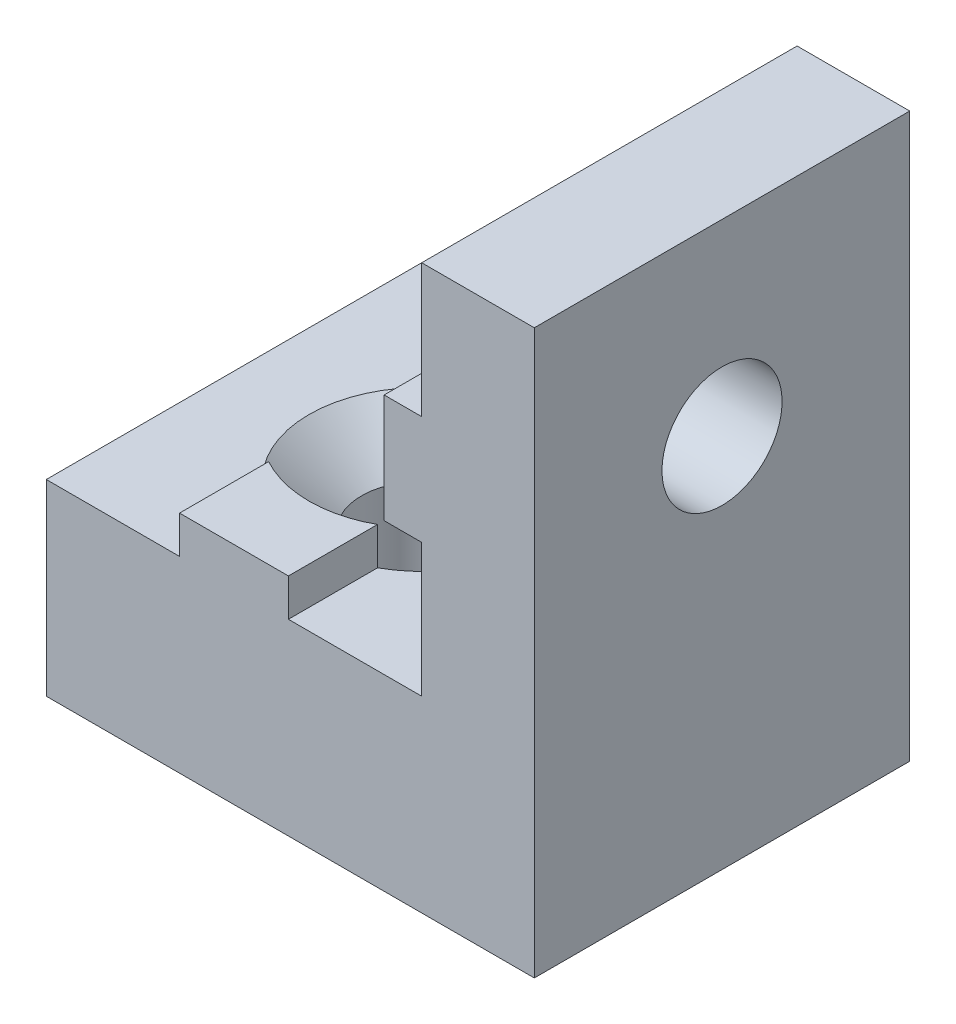
SolidWorks part; units mm, degrees
ref_plane "Front Plane" through (0, 0, 0) normal (0, 0, 1) x (1, 0, 0)
ref_plane "Top Plane" through (0, 0, 0) normal (0, 1, 0) x (1, 0, 0)
ref_plane "Right Plane" through (0, 0, 0) normal (1, 0, 0) x (0, 0, -1)
sketch "Esquisse1" plane through (0, 0, 0) normal (0, 0, 1) x (1, 0, 0)
  line L0 (0, 5) -> (3.55, 5)
  line L1 (3.55, 5) -> (3.55, 6)
  line L2 (3.55, 6) -> (6.45, 6)
  line L3 (6.45, 6) -> (6.45, 5)
  line L4 (6.45, 5) -> (10, 5)
  line L5 (10, 5) -> (10, 8.55)
  line L6 (10, 8.55) -> (9, 8.55)
  line L7 (9, 8.55) -> (9, 11.45)
  line L8 (9, 11.45) -> (10, 11.45)
  line L9 (10, 11.45) -> (10, 15)
  line L10 (10, 15) -> (13, 15)
  line L11 (13, 15) -> (13, 0)
  line L12 (13, 0) -> (0, 0)
  line L13 (0, 0) -> (0, 5)
  point P3 (-6.8358, -2.8214)
  point P15 (-7.4596, -3.1957)
  point P16 (-7.216, -1.6003)
  point P17 (0, 0)
  dimension "D1" = 3
  dimension "D2" = 3.55
  dimension "D3" = 2.9
  dimension "D4" = 5
  dimension "D5" = 1
extrude "Main" add sketch "Esquisse1" along normal blind 10
hole_wizard "Fraisage pour vis à tête fraisée (100) #01" positions "Esquisse3" profile "Esquisse4" countersink size "#0" standard "Ansi Inch"
sketch "Esquisse3" plane through (0, 5, 0) normal (0, 1, 0) x (1, 0, 0)
  line L0 (0, -10) -> (0, 0) construction
  line L1 (6.45, -10) -> (3.55, -10) construction
  point P0 (5, -5)
  dimension "D1" = 5
  dimension "D2" = 5
sketch "Esquisse4" plane through (5, 5, 5) normal (1, 0, 0) x (0, 0, 1)
  line L0 (0, 0) -> (0, 5)
  line L1 (0, 5) -> (1.6, 5)
  line L2 (1.6, 5) -> (1.6, 1.1747)
  line L3 (1.6, 1.1747) -> (3, 0)
  line L5 (3, 0) -> (0, 0)
  line L6 (-1.6, 1.1747) -> (-3, 0) construction
  line L11 (0, -6.35) -> (0, 107.95) construction
  dimension "Diamètre du perçage jusqu'au prochain" = 3.2
  dimension "Profondeur du perçage jusqu'au prochain" = 5
  dimension "Diamètre du fraisage entrant" = 6
  dimension "Angle du fraisage entrant" = 100
sketch "Esquisse5" plane through (0, 6, 0) normal (0, 1, 0) x (1, 0, 0)
  circle A0 centre (5, -5) radius 3
  arc A1 (6.45, -7.6263) -> (6.45, -2.3737) centre (5, -5) ccw construction
extrude "Enlèv. mat.-Extru.1" cut sketch "Esquisse5" against normal up to surface (1 mm away) up to face at (7.8917, 5, 5)
sketch "Esquisse6" plane through (9, 0, 0) normal (-1, 0, 0) x (0, 0, 1)
  line L0 (10, 11.45) -> (10, 8.55) construction
  line L1 (10, 15) -> (0, 15) construction
  circle A0 centre (5, 10) radius 1.6
  dimension "D1" = 3.2
  dimension "D2" = 5
  dimension "D3" = 5
extrude "Enlèv. mat.-Extru.2" cut sketch "Esquisse6" against normal through all
